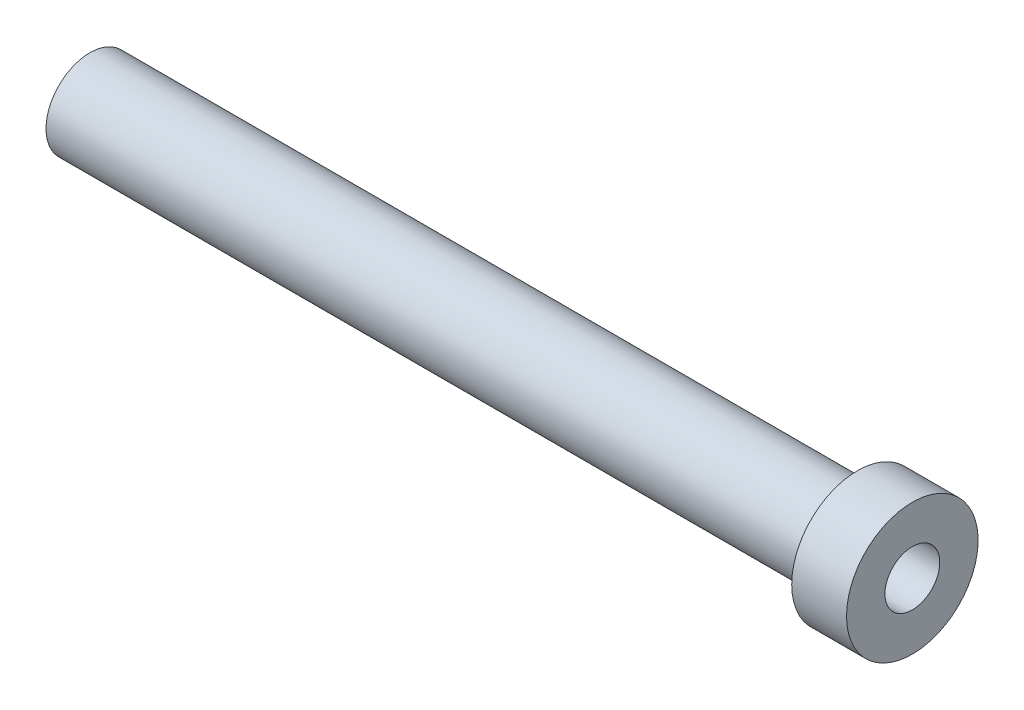
SolidWorks part; units mm, degrees
ref_plane "Спереди" through (0, 0, 0) normal (0, 0, 1) x (1, 0, 0)
ref_plane "Сверху" through (0, 0, 0) normal (0, 1, 0) x (1, 0, 0)
ref_plane "Справа" through (0, 0, 0) normal (1, 0, 0) x (0, 0, -1)
sketch "Эскиз1" plane through (0, 0, 0) normal (0, 0, 1) x (1, 0, 0)
  line L0 (0, 0) -> (112.9934, 0) construction
  line L1 (6.6612, 0) -> (6.6612, 4)
  line L2 (6.6612, 4) -> (76.6612, 4)
  line L3 (76.6612, 4) -> (76.6612, 6)
  line L4 (76.6612, 6) -> (81.6612, 6)
  line L5 (81.6612, 6) -> (81.6612, 0)
  line L6 (81.6612, 0) -> (6.6612, 0)
  dimension "D1" = 75
  dimension "D2" = 4
  dimension "D3" = 6
  dimension "D4" = 5
revolve "Повернуть1" add sketch "Эскиз1" angle 360 about L0
sketch "Эскиз2" plane through (81.6612, 0, 0) normal (1, 0, 0) x (0, 0, -1)
  circle A0 centre (0, 0) radius 2.5
  dimension "D1" = 5
extrude "Вырез-Вытянуть1" cut sketch "Эскиз2" against normal through all
